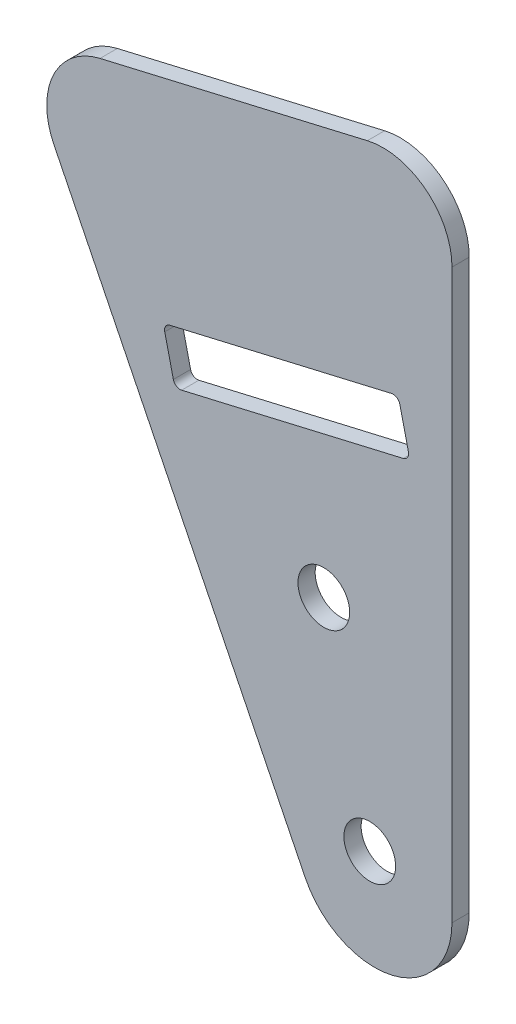
SolidWorks part; units mm, degrees
ref_plane "Front Plane" through (0, 0, 0) normal (0, 0, 1) x (1, 0, 0)
ref_plane "Top Plane" through (0, 0, 0) normal (0, 1, 0) x (1, 0, 0)
ref_plane "Right Plane" through (0, 0, 0) normal (1, 0, 0) x (0, 0, -1)
sketch "Sketch1" plane through (0, 0, 0) normal (0, 0, 1) x (1, 0, 0)
  line L0 (-20.0628, 730.2083) -> (-22.2273, 739.4841) construction
  line L1 (-63.35, 720.1077) -> (-65.5144, 729.3835) construction
  line L2 (-65.5144, 729.3835) -> (-22.2273, 739.4841) construction
  line L3 (-63.35, 720.1077) -> (-20.0628, 730.2083) construction
  line L4 (-20.0628, 730.2083) -> (-22.2273, 739.4841)
  line L5 (-63.35, 720.1077) -> (-65.5144, 729.3835)
  line L6 (-65.5144, 729.3835) -> (-22.2273, 739.4841)
  line L7 (-63.35, 720.1077) -> (-20.0628, 730.2083)
  line L8 (-27.4754, 664.1695) -> (-43.8708, 734.4338) construction
  line L9 (-43.8708, 734.4338) -> (-52.5285, 771.5371) construction
  line L10 (-27.9192, 777.2794) -> (-77.1379, 765.7948)
  line L11 (-85.6404, 747.8062) -> (-39.3636, 654.0435)
  line L12 (-27.4754, 664.1695) -> (-19.1198, 628.361) construction
  line L13 (-12.3333, 764.9117) -> (-12.3333, 660.3508)
  line L14 (-10.16, 738.6274) -> (-10.16, 644.5849) construction
  circle A0 centre (-35.9346, 700.4225) radius 4.7625 construction
  circle A1 centre (-27.4754, 664.1695) radius 4.7625 construction
  circle A2 centre (-35.9346, 700.4225) radius 4.7625
  circle A3 centre (-27.4754, 664.1695) radius 4.7625
  arc A4 (-12.3333, 764.9117) -> (-27.9192, 777.2794) centre (-25.0333, 764.9117) ccw
  arc A5 (-77.1379, 765.7948) -> (-85.6404, 747.8062) centre (-74.252, 753.427) ccw
  arc A6 (-39.3636, 654.0435) -> (-12.3333, 660.3508) centre (-26.5843, 660.3508) ccw
  point P18 (-12.3333, 780.9163)
  point P21 (-92.7238, 762.1579)
  dimension "D4" = 12.7
  dimension "D1" = 38.1
  dimension "D2" = 41.275
  dimension "D3" = 36.7704
extrude "Boss-Extrude1" add sketch "Sketch1" along normal blind 3.175 contours L11 A6 L13 A4 L10 A5 L7 L5 L6 L4 A2 A3
fillet "Fillet1" radius 1.27 4 edges at (-22.2273, 739.4841, 1.5875) (-65.5144, 729.3835, 1.5875) (-20.0628, 730.2083, 1.5875) (-63.35, 720.1077, 1.5875)
